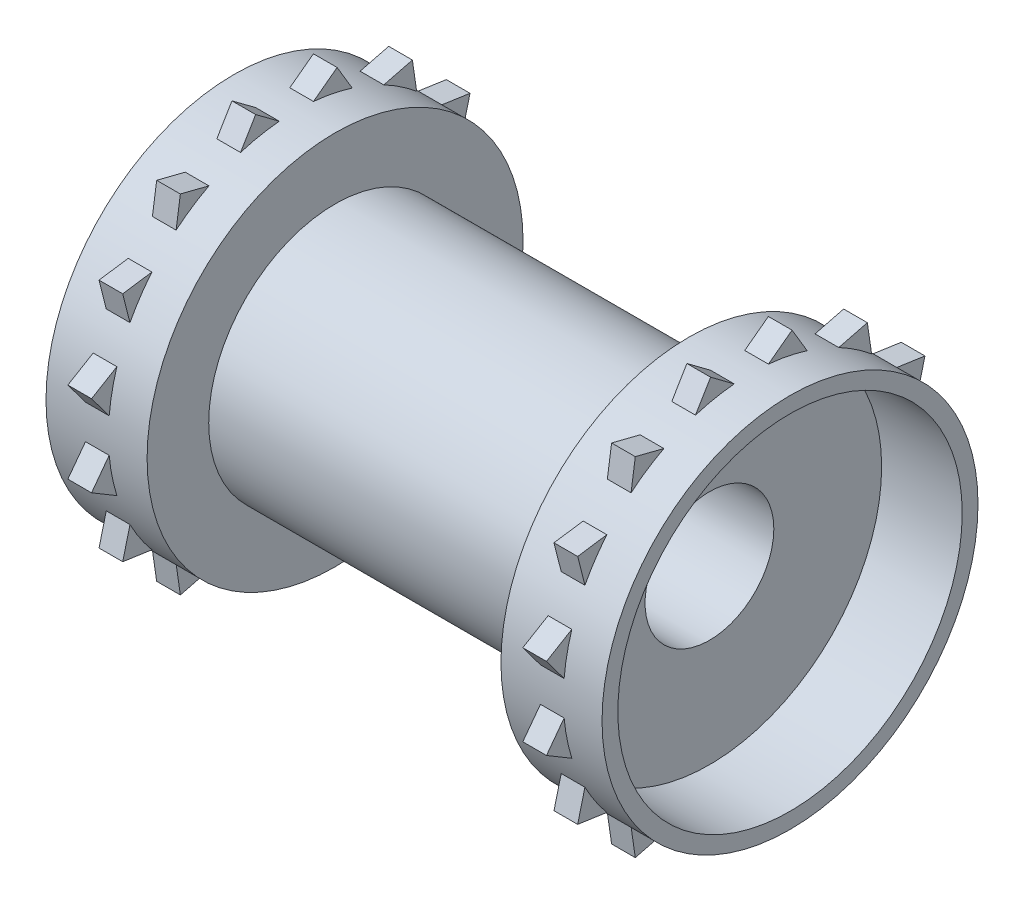
SolidWorks part; units mm, degrees
ref_plane "Alzado" through (0, 0, 0) normal (0, 0, 1) x (1, 0, 0)
ref_plane "Planta" through (0, 0, 0) normal (0, 1, 0) x (1, 0, 0)
ref_plane "Vista lateral" through (0, 0, 0) normal (1, 0, 0) x (0, 0, -1)
sketch "Croquis1" plane through (0, 0, 0) normal (1, 0, 0) x (0, 0, -1)
  line L0 (0, 0) -> (11.6713, 2.3216) construction
  line L2 (55, 0) -> (-55, 0) construction
  line L3 (0, 0) -> (11.6713, -2.3216) construction
  line L4 (0, 0) -> (9.8945, -6.6113) construction
  line L5 (0, 0) -> (6.6113, -9.8945) construction
  line L6 (0, 0) -> (2.3216, -11.6713) construction
  line L7 (0, 0) -> (-2.3216, -11.6713) construction
  line L8 (0, 0) -> (-6.6113, -9.8945) construction
  line L9 (0, 0) -> (-9.8945, -6.6113) construction
  line L10 (0, 0) -> (-11.6713, -2.3216) construction
  line L11 (0, 0) -> (-11.6713, 2.3216) construction
  line L12 (0, 0) -> (-9.8945, 6.6113) construction
  line L13 (0, 0) -> (-6.6113, 9.8945) construction
  line L14 (0, 0) -> (-2.3216, 11.6713) construction
  line L15 (0, 0) -> (2.3216, 11.6713) construction
  line L16 (0, 0) -> (6.6113, 9.8945) construction
  line L17 (0, 0) -> (9.8945, 6.6113) construction
  circle A0 centre (0, 0) radius 4.075
  circle A1 centre (0, 0) radius 11.9
  circle A2 centre (0, 0) radius 8
  point P24 (0, 0)
  dimension "D1" = 8.15
  dimension "D2" = 23.8
  dimension "D5" = 16
  dimension "D3" = 11.25
  dimension "D4" = 16
extrude "Saliente-Extruir1" add sketch "Croquis1" along normal mid plane 22.4 contours A2 A0
sketch "Croquis3" plane through (11.2, 0, 0) normal (1, 0, 0) x (0, 0, -1)
  circle A0 centre (0, 0) radius 11.9
  circle A1 centre (0, 0) radius 4.075
  circle A2 centre (0, 0) radius 4.075 construction
  circle A3 centre (0, 0) radius 11.9 construction
extrude "Saliente-Extruir2" add sketch "Croquis3" along normal blind 1.3
sketch "Croquis4" plane through (12.5, 0, 0) normal (1, 0, 0) x (0, 0, -1)
  circle A0 centre (0, 0) radius 11.9
  circle A1 centre (0, 0) radius 10.9
  circle A2 centre (0, 0) radius 11.9 construction
  dimension "D1" = 1
extrude "Saliente-Extruir3" add sketch "Croquis4" along normal blind 5.1
mirror "Simetría1" about plane through (0, 0, 0) normal (1, 0, 0) of "Saliente-Extruir3", "Saliente-Extruir2"
ref_plane "Plano1" through (14.4, 0, 0) normal (1, 0, 0) x (0, 0, -1)
sketch "Croquis5" plane through (14.4, 0, 0) normal (1, 0, 0) x (0, 0, -1)
  line L0 (2.3216, 11.6713) -> (2.5792, 12.9664) construction
  line L1 (2.5792, 12.9664) -> (3.5347, 11.3629)
  line L2 (7.3449, 10.9924) -> (7.614, 9.1453)
  line L3 (2.5792, 12.9664) -> (1.0827, 11.8506)
  line L4 (0, 0) -> (2.3216, 11.6713) construction
  line L5 (7.3449, 10.9924) -> (5.5354, 10.5342)
  line L6 (6.6113, 9.8945) -> (7.3449, 10.9924) construction
  line L7 (10.9924, 7.3449) -> (10.5342, 5.5354)
  line L8 (10.9924, 7.3449) -> (9.1453, 7.614)
  line L9 (9.8945, 6.6113) -> (10.9924, 7.3449) construction
  line L10 (12.9664, 2.5792) -> (11.8506, 1.0827)
  line L11 (12.9664, 2.5792) -> (11.3629, 3.5347)
  line L12 (11.6713, 2.3216) -> (12.9664, 2.5792) construction
  line L13 (12.9664, -2.5792) -> (11.3629, -3.5347)
  line L14 (12.9664, -2.5792) -> (11.8506, -1.0827)
  line L15 (11.6713, -2.3216) -> (12.9664, -2.5792) construction
  line L16 (10.9924, -7.3449) -> (9.1453, -7.614)
  line L17 (10.9924, -7.3449) -> (10.5342, -5.5354)
  line L18 (9.8945, -6.6113) -> (10.9924, -7.3449) construction
  line L19 (7.3449, -10.9924) -> (5.5354, -10.5342)
  line L20 (7.3449, -10.9924) -> (7.614, -9.1453)
  line L21 (6.6113, -9.8945) -> (7.3449, -10.9924) construction
  line L22 (2.5792, -12.9664) -> (1.0827, -11.8506)
  line L23 (2.5792, -12.9664) -> (3.5347, -11.3629)
  line L24 (2.3216, -11.6713) -> (2.5792, -12.9664) construction
  line L25 (-2.5792, -12.9664) -> (-3.5347, -11.3629)
  line L26 (-2.5792, -12.9664) -> (-1.0827, -11.8506)
  line L27 (-2.3216, -11.6713) -> (-2.5792, -12.9664) construction
  line L28 (-7.3449, -10.9924) -> (-7.614, -9.1453)
  line L29 (-7.3449, -10.9924) -> (-5.5354, -10.5342)
  line L30 (-6.6113, -9.8945) -> (-7.3449, -10.9924) construction
  line L31 (-10.9924, -7.3449) -> (-10.5342, -5.5354)
  line L32 (-10.9924, -7.3449) -> (-9.1453, -7.614)
  line L33 (-9.8945, -6.6113) -> (-10.9924, -7.3449) construction
  line L34 (-12.9664, -2.5792) -> (-11.8506, -1.0827)
  line L35 (-12.9664, -2.5792) -> (-11.3629, -3.5347)
  line L36 (-11.6713, -2.3216) -> (-12.9664, -2.5792) construction
  line L37 (-12.9664, 2.5792) -> (-11.3629, 3.5347)
  line L38 (-12.9664, 2.5792) -> (-11.8506, 1.0827)
  line L39 (-11.6713, 2.3216) -> (-12.9664, 2.5792) construction
  line L40 (-10.9924, 7.3449) -> (-9.1453, 7.614)
  line L41 (-10.9924, 7.3449) -> (-10.5342, 5.5354)
  line L42 (-9.8945, 6.6113) -> (-10.9924, 7.3449) construction
  line L43 (-7.3449, 10.9924) -> (-5.5354, 10.5342)
  line L44 (-7.3449, 10.9924) -> (-7.614, 9.1453)
  line L45 (-6.6113, 9.8945) -> (-7.3449, 10.9924) construction
  line L46 (-2.5792, 12.9664) -> (-1.0827, 11.8506)
  line L47 (-2.5792, 12.9664) -> (-3.5347, 11.3629)
  line L48 (-2.3216, 11.6713) -> (-2.5792, 12.9664) construction
  arc A0 (1.0827, 11.8506) -> (3.5347, 11.3629) centre (0, 0) cw
  circle A1 centre (0, 0) radius 11.9 construction
  arc A2 (5.5354, 10.5342) -> (7.614, 9.1453) centre (0, 0) cw
  arc A3 (9.1453, 7.614) -> (10.5342, 5.5354) centre (0, 0) cw
  arc A4 (11.3629, 3.5347) -> (11.8506, 1.0827) centre (0, 0) cw
  arc A5 (11.8506, -1.0827) -> (11.3629, -3.5347) centre (0, 0) cw
  arc A6 (10.5342, -5.5354) -> (9.1453, -7.614) centre (0, 0) cw
  arc A7 (7.614, -9.1453) -> (5.5354, -10.5342) centre (0, 0) cw
  arc A8 (3.5347, -11.3629) -> (1.0827, -11.8506) centre (0, 0) cw
  arc A9 (-1.0827, -11.8506) -> (-3.5347, -11.3629) centre (0, 0) cw
  arc A10 (-5.5354, -10.5342) -> (-7.614, -9.1453) centre (0, 0) cw
  arc A11 (-9.1453, -7.614) -> (-10.5342, -5.5354) centre (0, 0) cw
  arc A12 (-11.3629, -3.5347) -> (-11.8506, -1.0827) centre (0, 0) cw
  arc A13 (-11.8506, 1.0827) -> (-11.3629, 3.5347) centre (0, 0) cw
  arc A14 (-10.5342, 5.5354) -> (-9.1453, 7.614) centre (0, 0) cw
  arc A15 (-7.614, 9.1453) -> (-5.5354, 10.5342) centre (0, 0) cw
  arc A16 (-3.5347, 11.3629) -> (-1.0827, 11.8506) centre (0, 0) cw
  point P6 (2.3216, 11.6713)
  point P74 (0, 0)
  dimension "D1" = 1.3205
  dimension "D2" = 2.5
  dimension "D3" = 16
extrude "Saliente-Extruir4" add sketch "Croquis5" along normal mid plane 1.5
mirror "Simetría2" about plane through (0, 0, 0) normal (1, 0, 0) of "Saliente-Extruir4"
sketch "Croquis6" plane through (0, 0, 0) normal (0, 0, 1) x (1, 0, 0)
  circle A0 centre (0, 0) radius 2.5
  dimension "D1" = 5
extrude "Cortar-Extruir1" cut sketch "Croquis6" against normal through all
equation "\"D3@Croquis1\"=180/16"
equation "\"D2@Croquis1\"=23.8"
